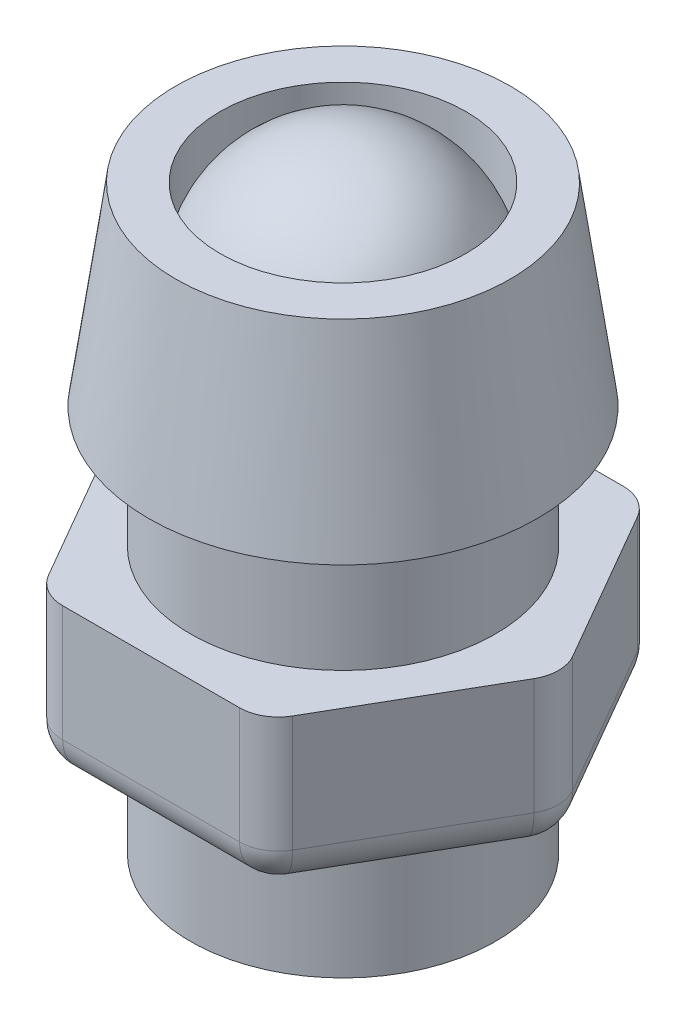
SolidWorks part; units mm, degrees
ref_plane "Front Plane" through (0, 0, 0) normal (0, 0, 1) x (1, 0, 0)
ref_plane "Top Plane" through (0, 0, 0) normal (0, 1, 0) x (1, 0, 0)
ref_plane "Right Plane" through (0, 0, 0) normal (1, 0, 0) x (0, 0, -1)
sketch "Sketch1" plane through (0, 0, 0) normal (0, 0, 1) x (1, 0, 0)
  line L0 (0, 0) -> (0, 15)
  line L1 (0, 15) -> (4.318, 15)
  line L2 (4.318, 15) -> (5.0207, 10)
  line L3 (5.0207, 10) -> (3.937, 10)
  line L4 (3.937, 10) -> (3.937, 0)
  line L5 (3.937, 0) -> (0, 0)
  line L6 (0, 0) -> (0, 105.5188) construction
  dimension "D1" = 7.874
  dimension "D2" = 8
  dimension "D3" = 15
  dimension "D4" = 5
  dimension "D5" = 8.636
revolve "Revolve1" add sketch "Sketch1" angle 360 about L6
sketch "Sketch2" plane through (0, 15, 0) normal (0, 1, 0) x (1, 0, 0)
  circle A0 centre (0, 0) radius 3.175
  dimension "D1" = 6.35
extrude "Cut-Extrude1" cut sketch "Sketch2" against normal through all
sketch "Sketch3" plane through (0, 0, 0) normal (0, 0, 1) x (1, 0, 0)
  line L0 (3.175, 0) -> (3.175, 15) construction
  line L1 (0, 0) -> (0, 18.8194) construction
  line L2 (-3.937, 0) -> (3.937, 0) construction
  line L3 (0, 16) -> (0, 13.5997)
  line L4 (0, 13.5997) -> (3.175, 13.5997)
  line L5 (3.175, 15) -> (-3.175, 15) construction
  arc A0 (0, 16) -> (3.175, 13.5997) centre (0, 12.7) cw
  dimension "D1" = 3.3
  dimension "D2" = 1
revolve "Revolve2" add sketch "Sketch3" angle 360 about L1
ref_plane "Plane1" through (0, 6.875, 0) normal (0, -1, 0) x (-1, 0, 0)
sketch "Sketch4" plane through (0, 6.875, 0) normal (0, -1, 0) x (-1, 0, 0)
  line L1 (5.7192, 0) -> (2.8596, 4.953)
  line L2 (2.8596, 4.953) -> (-2.8596, 4.953)
  line L3 (-2.8596, 4.953) -> (-5.7192, 0)
  line L4 (-5.7192, 0) -> (-2.8596, -4.953)
  line L5 (-2.8596, -4.953) -> (2.8596, -4.953)
  line L6 (2.8596, -4.953) -> (5.7192, 0)
  circle A0 centre (0, 0) radius 4.953 construction
  dimension "D1" = 9.906
extrude "Boss-Extrude1" add sketch "Sketch4" along normal blind 4
fillet "Fillet1" radius 1 6 edges at (5.7192, 4.875, 0) (2.8596, 4.875, -4.953) (-2.8596, 4.875, -4.953) (-5.7192, 4.875, 0) (-2.8596, 4.875, 4.953) (2.8596, 4.875, 4.953)
fillet "Fillet2" radius 1 12 edges at (-2.7823, 2.875, -4.819) (-4.2894, 2.875, -2.4765) (-5.5645, 2.875, 0) (-4.2894, 2.875, 2.4765) (-2.7823, 2.875, 4.819) (0, 2.875, 4.953) (2.7823, 2.875, 4.819) (4.2894, 2.875, 2.4765) (5.5645, 2.875, 0) (4.2894, 2.875, -2.4765) (2.7823, 2.875, -4.819) (0, 2.875, -4.953)
